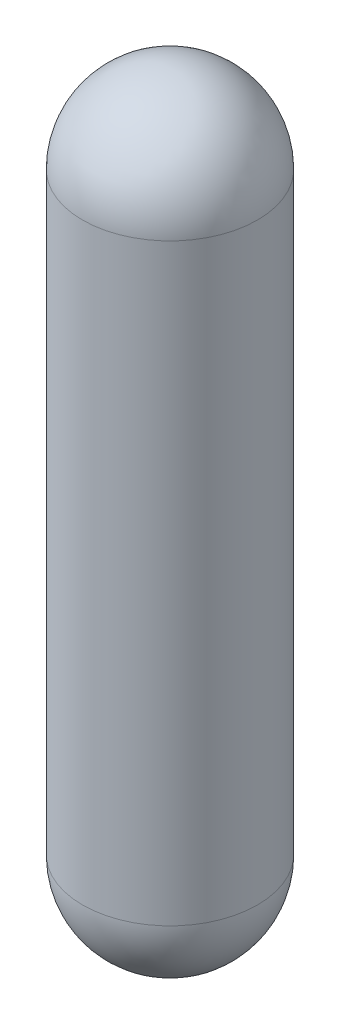
SolidWorks part; units mm, degrees
ref_plane "Front Plane" through (0, 0, 0) normal (0, 0, 1) x (1, 0, 0)
ref_plane "Top Plane" through (0, 0, 0) normal (0, 1, 0) x (1, 0, 0)
ref_plane "Right Plane" through (0, 0, 0) normal (1, 0, 0) x (0, 0, -1)
sketch "Sketch1" plane through (0, 0, 0) normal (0, 0, 1) x (1, 0, 0)
  line L0 (0, 43.5) -> (0, -43.5)
  line L1 (12.8333, 43.5) -> (12.8333, -43.5)
  line L3 (0, 43.5) -> (0, 56.3333)
  line L4 (0, -43.5) -> (0, -56.3333)
  arc A0 (12.8333, 43.5) -> (0, 56.3333) centre (0, 43.5) ccw
  arc A1 (0, -56.3333) -> (12.8333, -43.5) centre (0, -43.5) ccw
  point P4 (0, 0)
  dimension "D2" = 25.6667
  dimension "D3" = 25.6667
  dimension "D1" = 87
revolve "Revolve1" add sketch "Sketch1" angle 360 about L0
